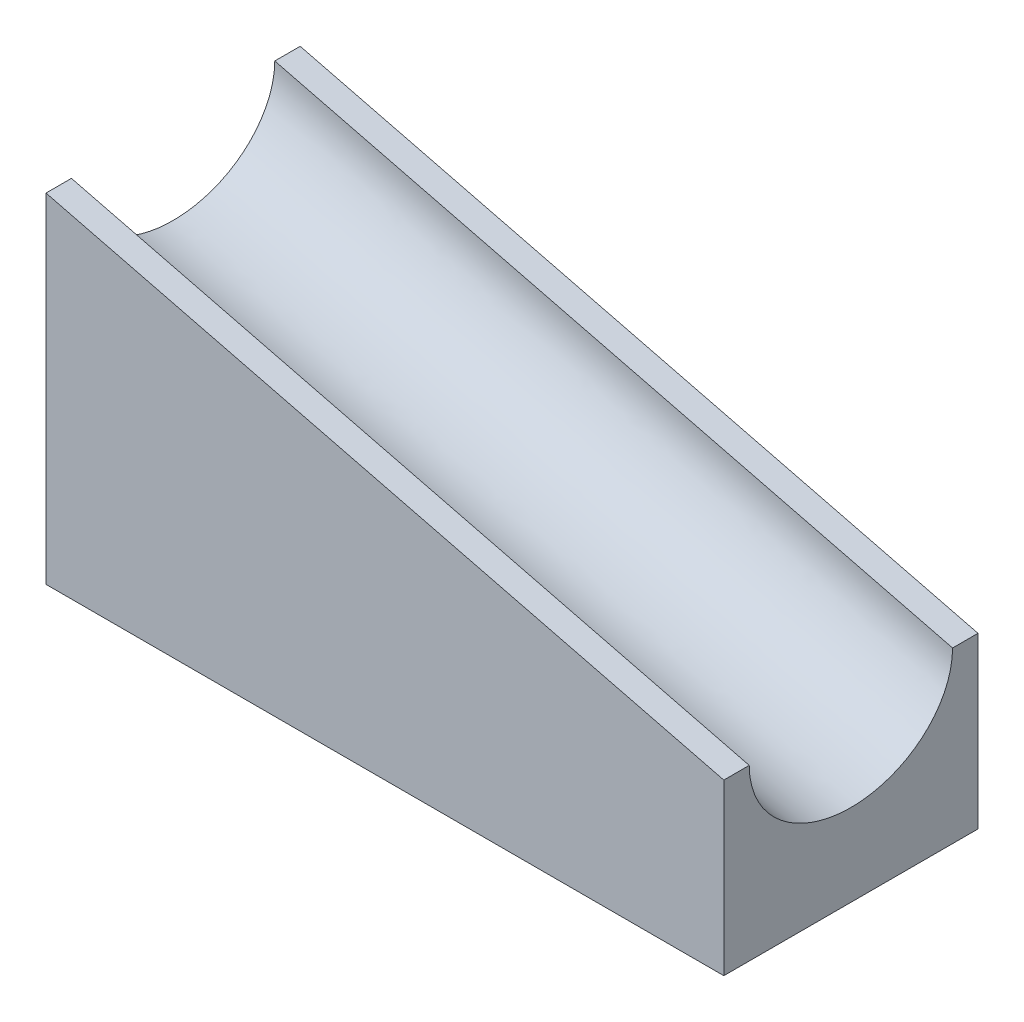
SolidWorks part; units mm, degrees
ref_plane "Front Plane" through (0, 0, 0) normal (0, 0, 1) x (1, 0, 0)
ref_plane "Top Plane" through (0, 0, 0) normal (0, 1, 0) x (1, 0, 0)
ref_plane "Right Plane" through (0, 0, 0) normal (1, 0, 0) x (0, 0, -1)
sketch "Sketch1" plane through (0, 0, 0) normal (0, 0, 1) x (1, 0, 0)
  line L0 (-25.4, 12.7) -> (-25.4, -12.7)
  line L1 (-25.4, -12.7) -> (25.4, -12.7)
  line L2 (25.4, -12.7) -> (25.4, 0)
  line L3 (25.4, 0) -> (-25.4, 12.7)
  point P2 (-25.4, 0)
  point P5 (0, -12.7)
  dimension "D1" = 25.4
  dimension "D2" = 50.8
  dimension "D3" = 12.7
extrude "Boss-Extrude1" add sketch "Sketch1" along normal blind 19.05
ref_plane "Plane1" through (-26.8941, 6.7235, 0) normal (-0.9701, 0.2425, 0) x (0, 0, -1)
sketch "Sketch3" plane through (-26.8941, 6.7235, 0) normal (-0.9701, 0.2425, 0) x (0, 0, -1)
  line L0 (-19.05, -6.1604) -> (0, -6.1604) construction
  ellipse E0 centre (-9.525, -6.1604) end of major axis (-1.905, -6.1604) minor radius 6.35
  dimension "D1" = 7.62
  dimension "D2" = 6.35
extrude "Cut-Extrude1" cut sketch "Sketch3" against normal through all
